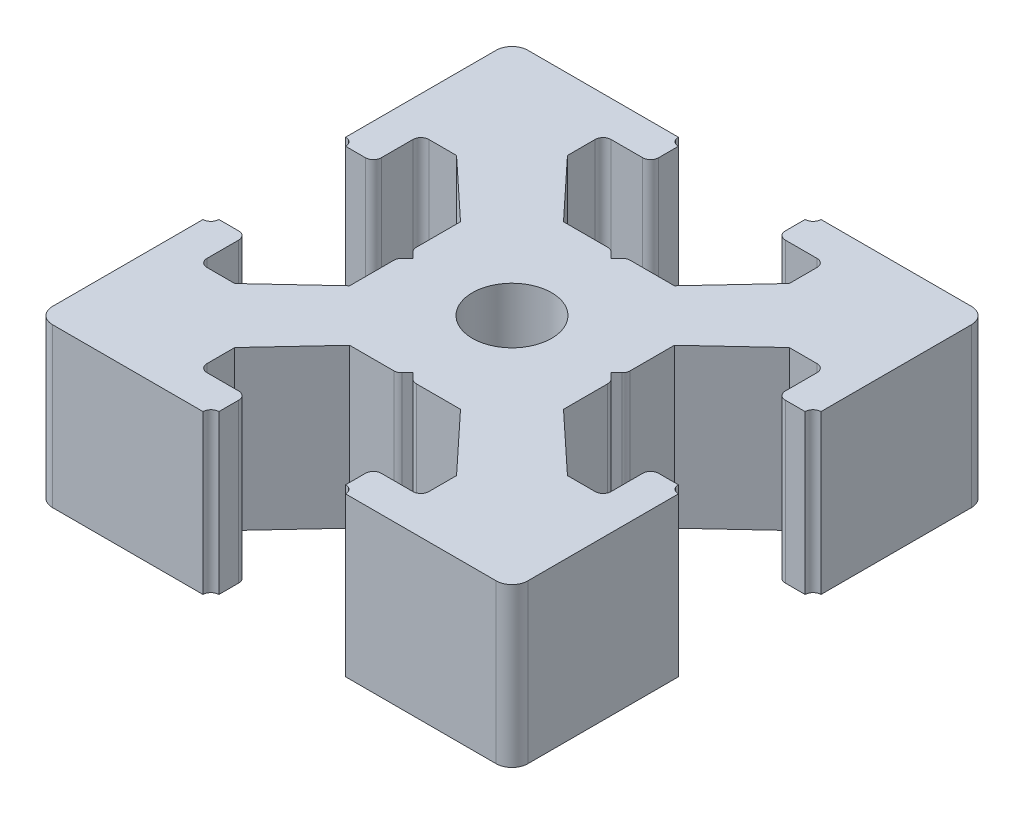
SolidWorks part; units mm, degrees
ref_plane "Front Plane" through (0, 0, 0) normal (0, 0, 1) x (1, 0, 0)
ref_plane "Top Plane" through (0, 0, 0) normal (0, 1, 0) x (1, 0, 0)
ref_plane "Right Plane" through (0, 0, 0) normal (1, 0, 0) x (0, 0, -1)
sketch "Sketch3" plane through (0, 0, 0) normal (0, 1, 0) x (1, 0, 0)
  line L0 (11, 30) -> (11, 27.75)
  line L1 (0, 0) -> (30, 0)
  line L2 (0, 0) -> (0, 30)
  line L3 (0, 30) -> (30, 30)
  line L4 (30, 0) -> (30, 30)
  line L5 (11, 27.75) -> (8, 27.75)
  line L6 (8, 27.75) -> (8, 25.5)
  line L7 (8, 25.5) -> (11.5, 21.75)
  line L8 (11.5, 21.75) -> (18.5, 21.75)
  line L9 (18.5, 21.75) -> (22, 25.5)
  line L10 (22, 25.5) -> (22, 27.75)
  line L11 (22, 27.75) -> (19, 27.75)
  line L12 (19, 27.75) -> (19, 30)
  line L13 (19, 30) -> (11, 30)
  line L14 (14.5, 21.75) -> (15, 21.25)
  line L15 (15, 21.25) -> (15.5, 21.75)
  line L16 (15.5, 21.75) -> (14.5, 21.75)
  line L17 (19, 29.5) -> (19, 30)
  line L18 (19.5, 30) -> (19, 30)
  line L19 (11, 29.5) -> (11, 30)
  line L20 (10.5, 30) -> (11, 30)
  line L21 (0, 19) -> (2.25, 19)
  line L22 (2.25, 19) -> (2.25, 22)
  line L23 (2.25, 22) -> (4.5, 22)
  line L24 (4.5, 22) -> (8.25, 18.5)
  line L25 (8.25, 18.5) -> (8.25, 11.5)
  line L26 (8.25, 11.5) -> (4.5, 8)
  line L27 (4.5, 8) -> (2.25, 8)
  line L28 (2.25, 8) -> (2.25, 11)
  line L29 (2.25, 11) -> (0, 11)
  line L30 (0, 11) -> (0, 19)
  line L31 (8.25, 15.5) -> (8.25, 14.5)
  line L32 (8.25, 14.5) -> (8.75, 15)
  line L33 (8.75, 15) -> (8.25, 15.5)
  line L34 (0.5, 19) -> (0, 19)
  line L35 (0, 19.5) -> (0, 19)
  line L36 (0, 10.5) -> (0, 11)
  line L37 (0.5, 11) -> (0, 11)
  line L38 (15, 30) -> (15, 0) construction
  line L39 (30, 15) -> (0, 15) construction
  line L40 (15, 8.75) -> (15.5, 8.25)
  line L41 (14.5, 8.25) -> (15, 8.75)
  line L42 (15.5, 8.25) -> (14.5, 8.25)
  line L43 (19.5, 0) -> (19, 0)
  line L44 (19, 0.5) -> (19, 0)
  line L45 (10.5, 0) -> (11, 0)
  line L46 (11, 0.5) -> (11, 0)
  line L47 (19, 2.25) -> (19, 0)
  line L48 (22, 2.25) -> (19, 2.25)
  line L49 (22, 4.5) -> (22, 2.25)
  line L50 (18.5, 8.25) -> (22, 4.5)
  line L51 (11.5, 8.25) -> (18.5, 8.25)
  line L52 (8, 4.5) -> (11.5, 8.25)
  line L53 (8, 2.25) -> (8, 4.5)
  line L54 (11, 2.25) -> (8, 2.25)
  line L55 (11, 0) -> (11, 2.25)
  line L56 (19, 0) -> (11, 0)
  line L57 (21.75, 14.5) -> (21.25, 15)
  line L58 (21.75, 15.5) -> (21.75, 14.5)
  line L59 (21.25, 15) -> (21.75, 15.5)
  line L60 (29.5, 11) -> (30, 11)
  line L61 (30, 10.5) -> (30, 11)
  line L62 (30, 19.5) -> (30, 19)
  line L63 (29.5, 19) -> (30, 19)
  line L64 (27.75, 11) -> (30, 11)
  line L65 (27.75, 8) -> (27.75, 11)
  line L66 (25.5, 8) -> (27.75, 8)
  line L67 (21.75, 11.5) -> (25.5, 8)
  line L68 (21.75, 18.5) -> (21.75, 11.5)
  line L69 (25.5, 22) -> (21.75, 18.5)
  line L70 (27.75, 22) -> (25.5, 22)
  line L71 (27.75, 19) -> (27.75, 22)
  line L72 (30, 19) -> (27.75, 19)
  line L73 (30, 11) -> (30, 19)
  arc A0 (19.5, 30) -> (19, 29.5) centre (19, 30) cw
  arc A1 (10.5, 30) -> (11, 29.5) centre (11, 30) ccw
  arc A2 (0.5, 19) -> (0, 19.5) centre (0, 19) ccw
  arc A3 (0.5, 11) -> (0, 10.5) centre (0, 11) cw
  arc A4 (19.5, 0) -> (19, 0.5) centre (19, 0) ccw
  arc A5 (10.5, 0) -> (11, 0.5) centre (11, 0) cw
  arc A6 (29.5, 11) -> (30, 10.5) centre (30, 11) ccw
  arc A7 (29.5, 19) -> (30, 19.5) centre (30, 19) cw
  point P7 (15, 21.75)
  point P16 (15, 30)
  point P26 (8.25, 15)
  point P35 (0, 15)
  dimension "D16" = 0.5
  dimension "D17" = 0.5
  dimension "D28" = 0.5
  dimension "D29" = 0.5
  dimension "D1" = 30
  dimension "D2" = 30
  dimension "D3" = 11
  dimension "D4" = 11
  dimension "D5" = 2.25
  dimension "D6" = 2.25
  dimension "D7" = 3
  dimension "D8" = 3
  dimension "D9" = 2.25
  dimension "D10" = 2.25
  dimension "D11" = 7
  dimension "D12" = 8.25
  dimension "D13" = 0.5
  dimension "D14" = 0.5
  dimension "D15" = 0.5
  dimension "D18" = 11
  dimension "D19" = 11
  dimension "D20" = 2.25
  dimension "D21" = 2.25
  dimension "D22" = 3
  dimension "D23" = 7
  dimension "D24" = 8.25
  dimension "D25" = 0.5
  dimension "D26" = 0.5
  dimension "D27" = 0.5
extrude "Boss-Extrude1" add sketch "Sketch3" along normal blind 10 contours L72 A7 L4 L3 A0 L12 L11 L10 L9 L8 L15 L14 L7 L6 L5 L0 A1 L2 A2 L21 L22 L23 L24 L25 L33 L32 L26 L27 L28 L29 A3 L1 A5 L55 L54 L53 L52 L51 L41 L40 L50 L49 L48 L47 A4
fillet "Fillet1" radius 1 4 edges at (0, 5, 0) (30, 5, 0) (30, 5, -30) (0, 5, -30)
sketch "Sketch4" plane through (0, 10, 0) normal (0, 1, 0) x (1, 0, 0)
  line L0 (18.5, 21.75) -> (8.25, 11.5) construction
  line L1 (21.75, 18.5) -> (11.5, 8.25) construction
  line L2 (15.5, 21.75) -> (21.75, 15.5) construction
  line L9 (8.25, 14.5) -> (14.5, 8.25) construction
  line L10 (8.25, 15.5) -> (14.5, 21.75) construction
  line L11 (21.75, 14.5) -> (15.5, 8.25) construction
  line L12 (11.5, 21.75) -> (21.75, 11.5) construction
  line L13 (8.25, 18.5) -> (18.5, 8.25) construction
  line L20 (30, 15) -> (0, 15) construction
  circle A0 centre (15, 15) radius 2.5
  dimension "D1" = 5
extrude "Cut-Extrude1" cut sketch "Sketch4" against normal through all
fillet "Fillet2" radius 0.5 24 edges at (2.25, 5, -22) (2.25, 5, -19) (8.25, 5, -15.5) (8.25, 5, -14.5) (2.25, 5, -11) (2.25, 5, -8) (8, 5, -2.25) (11, 5, -2.25) (14.5, 5, -8.25) (15.5, 5, -8.25) (19, 5, -2.25) (22, 5, -2.25) (27.75, 5, -8) (27.75, 5, -11) (27.75, 5, -19) (27.75, 5, -22) (21.75, 5, -14.5) (21.75, 5, -15.5) (15.5, 5, -21.75) (14.5, 5, -21.75) (22, 5, -27.75) (19, 5, -27.75) (11, 5, -27.75) (8, 5, -27.75)
